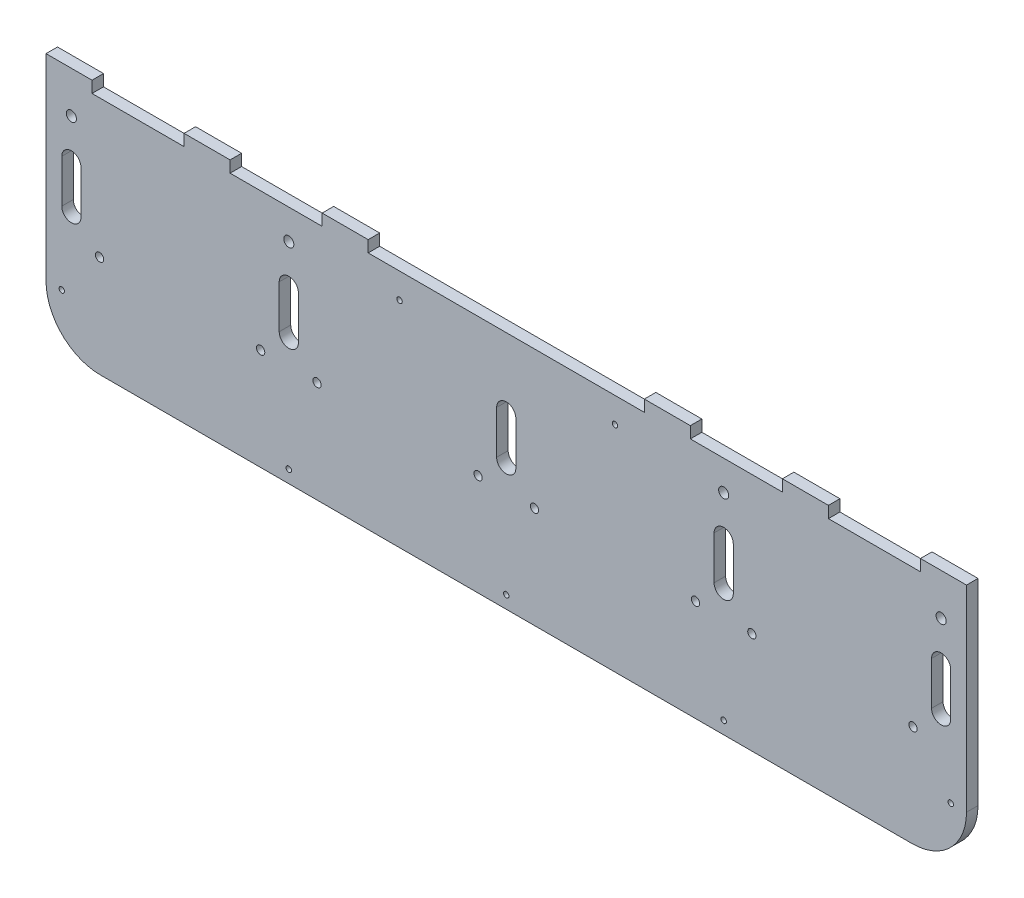
SolidWorks part; units mm, degrees
ref_plane "Front Plane" through (0, 0, 0) normal (0, 0, 1) x (1, 0, 0)
ref_plane "Top Plane" through (0, 0, 0) normal (0, 1, 0) x (1, 0, 0)
ref_plane "Right Plane" through (0, 0, 0) normal (1, 0, 0) x (0, 0, -1)
sketch "Sketch1" plane through (0, 0, 0) normal (0, 0, 1) x (1, 0, 0)
  line L1 (-491.3302, -1.4434) -> (-491.3302, -103.6809)
  line L2 (-465.9302, -1.4434) -> (-415.1302, -1.4434)
  line L3 (16.6698, -1.4434) -> (16.6698, -103.6809)
  line L4 (-13.3302, -133.6809) -> (-461.3302, -133.6809)
  line L19 (16.6698, -1.4434) -> (16.6698, 4.9066)
  line L20 (16.6698, 4.9066) -> (-8.7302, 4.9066)
  line L21 (-8.7302, 4.9066) -> (-8.7302, -1.4434)
  line L22 (-59.5302, -1.4434) -> (-59.5302, 4.9066)
  line L23 (-59.5302, 4.9066) -> (-84.9302, 4.9066)
  line L24 (-84.9302, 4.9066) -> (-84.9302, -1.4434)
  line L25 (-135.7302, -1.4434) -> (-135.7302, 4.9066)
  line L26 (-135.7302, 4.9066) -> (-161.1302, 4.9066)
  line L27 (-161.1302, 4.9066) -> (-161.1302, -1.4434)
  line L28 (-491.3302, -1.4434) -> (-491.3302, 4.9066)
  line L29 (-491.3302, 4.9066) -> (-465.9302, 4.9066)
  line L30 (-465.9302, 4.9066) -> (-465.9302, -1.4434)
  line L31 (-415.1302, -1.4434) -> (-415.1302, 4.9066)
  line L32 (-415.1302, 4.9066) -> (-389.7302, 4.9066)
  line L33 (-389.7302, 4.9066) -> (-389.7302, -1.4434)
  line L34 (-338.9302, -1.4434) -> (-338.9302, 4.9066)
  line L35 (-338.9302, 4.9066) -> (-313.5302, 4.9066)
  line L36 (-313.5302, 4.9066) -> (-313.5302, -1.4434)
  line L37 (-389.7302, -1.4434) -> (-338.9302, -1.4434)
  line L38 (-313.5302, -1.4434) -> (-161.1302, -1.4434)
  line L39 (-59.5302, -1.4434) -> (-8.7302, -1.4434)
  line L40 (-135.7302, -1.4434) -> (-84.9302, -1.4434)
  line L41 (-237.3302, -39.8132) -> (-237.3302, -63.6486) construction
  line L42 (-232.0344, -39.8132) -> (-232.0344, -63.6486)
  line L43 (-117.3302, -39.8132) -> (-117.3302, -63.6486) construction
  line L44 (-112.0344, -39.8132) -> (-112.0344, -63.6486)
  line L45 (-122.6261, -39.8132) -> (-122.6261, -63.6486)
  line L46 (-242.6261, -39.8132) -> (-242.6261, -63.6486)
  line L47 (-357.3302, -39.8132) -> (-357.3302, -63.6486) construction
  line L48 (-352.0344, -39.8132) -> (-352.0344, -63.6486)
  line L49 (-362.6261, -39.8132) -> (-362.6261, -63.6486)
  line L50 (-477.3302, -39.8132) -> (-477.3302, -63.6486) construction
  line L51 (-472.0344, -39.8132) -> (-472.0344, -63.6486)
  line L52 (-482.6261, -39.8132) -> (-482.6261, -63.6486)
  line L53 (2.6698, -39.8132) -> (2.6698, -63.6486) construction
  line L54 (7.9656, -39.8132) -> (7.9656, -63.6486)
  line L55 (-2.6261, -39.8132) -> (-2.6261, -63.6486)
  arc A18 (16.6698, -103.6809) -> (-13.3302, -133.6809) centre (-13.3302, -103.6809) cw
  arc A19 (-491.3302, -103.6809) -> (-461.3302, -133.6809) centre (-461.3302, -103.6809) ccw
  circle A29 centre (-461.7802, -77.5622) radius 2.286
  circle A32 centre (-372.8802, -77.5622) radius 2.286
  circle A33 centre (-341.7802, -77.5622) radius 2.286
  circle A34 centre (-252.8802, -77.5622) radius 2.286
  circle A35 centre (-221.7802, -77.5622) radius 2.286
  circle A36 centre (-132.8802, -77.5622) radius 2.286
  circle A37 centre (-101.7802, -77.5622) radius 2.286
  circle A38 centre (-12.8802, -77.5622) radius 2.286
  arc A39 (-112.0344, -39.8132) -> (-122.6261, -39.8132) centre (-117.3302, -39.8132) ccw
  arc A40 (-122.6261, -63.6486) -> (-112.0344, -63.6486) centre (-117.3302, -63.6486) ccw
  arc A41 (-232.0344, -39.8132) -> (-242.6261, -39.8132) centre (-237.3302, -39.8132) ccw
  arc A42 (-242.6261, -63.6486) -> (-232.0344, -63.6486) centre (-237.3302, -63.6486) ccw
  arc A43 (-352.0344, -39.8132) -> (-362.6261, -39.8132) centre (-357.3302, -39.8132) ccw
  arc A44 (-362.6261, -63.6486) -> (-352.0344, -63.6486) centre (-357.3302, -63.6486) ccw
  arc A45 (-472.0344, -39.8132) -> (-482.6261, -39.8132) centre (-477.3302, -39.8132) ccw
  arc A46 (-482.6261, -63.6486) -> (-472.0344, -63.6486) centre (-477.3302, -63.6486) ccw
  arc A47 (7.9656, -39.8132) -> (-2.6261, -39.8132) centre (2.6698, -39.8132) ccw
  arc A48 (-2.6261, -63.6486) -> (7.9656, -63.6486) centre (2.6698, -63.6486) ccw
  circle A49 centre (-117.3302, -126.7215) radius 1.5
  circle A50 centre (-237.3302, -126.7215) radius 1.5
  circle A51 centre (-357.3302, -126.7215) radius 1.5
  circle A52 centre (-177.3302, -15.4134) radius 1.5
  circle A53 centre (-296.2217, -15.4134) radius 1.5
  circle A54 centre (2.6698, -17.9534) radius 2.794
  circle A55 centre (7.9656, -103.6809) radius 1.5
  circle A56 centre (-482.6261, -103.6809) radius 1.5
  circle A57 centre (-117.3302, -17.9534) radius 2.794
  circle A58 centre (-357.3302, -17.9534) radius 2.794
  circle A59 centre (-477.3302, -17.9534) radius 2.794
  point P28 (-491.3302, -52.5622)
  point P137 (-117.3302, -51.7309)
  point P144 (-237.3302, -51.7309)
  point P151 (-357.3302, -51.7309)
  point P158 (-477.3302, -51.7309)
  point P164 (2.6698, -51.7309)
  point P184 (-236.1872, -51.7309)
  dimension "D3" = 30
  dimension "D4" = 30
  dimension "D5" = 3
  dimension "D6" = 3
extrude "Boss-Extrude1" add sketch "Sketch1" along normal blind 6.35
